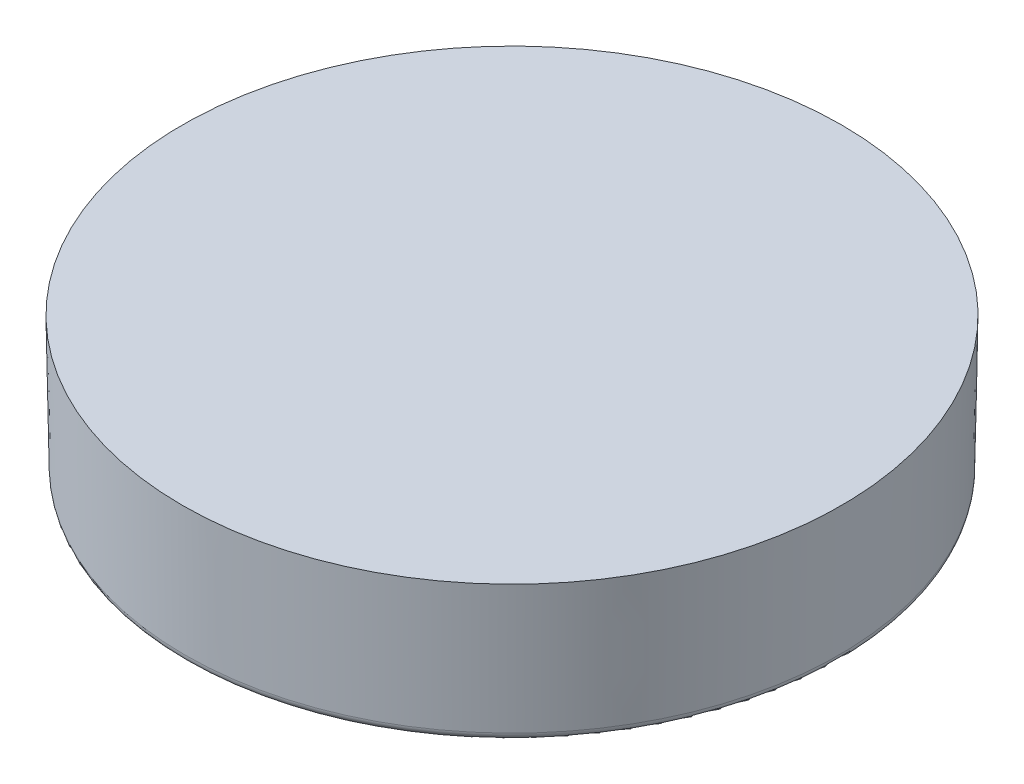
SolidWorks part; units mm, degrees
material "CA"
ref_plane "Front Plane" through (0, 0, 0) normal (0, 0, 1) x (1, 0, 0)
ref_plane "Top Plane" through (0, 0, 0) normal (0, 1, 0) x (1, 0, 0)
ref_plane "Right Plane" through (0, 0, 0) normal (1, 0, 0) x (0, 0, -1)
sketch "Sketch1" plane through (0, 0, 0) normal (0, 1, 0) x (1, 0, 0)
  circle A0 centre (0, 0) radius 15.0813
  dimension "D1" = 30.1625
extrude "Boss-Extrude1" add sketch "Sketch1" against normal blind 2.3114 draft 1
sketch "Sketch6" plane through (0, 0, 0) normal (0, 0, 1) x (1, 0, 0)
  line L0 (0, 0) -> (0, -2.54) construction
  line L1 (0, -2.54) -> (-6.985, -9.525)
  line L2 (0, -2.54) -> (6.985, -9.525)
  line L3 (-6.985, -9.525) -> (6.985, -9.525)
  line L5 (15.0813, 0) -> (-15.0813, 0) construction
  dimension "D1" = 2.54
  dimension "D2" = 90
  dimension "D3" = 9.525
sketch "Sketch7" plane through (0, 0, 0) normal (0, 1, 0) x (1, 0, 0)
  circle A1 centre (0, 0) radius 15.0813
  circle A2 centre (0, 0) radius 15.0813
  circle A3 centre (0, 0) radius 13.3033
  circle A4 centre (0, 0) radius 13.3033
  dimension "D1" = 0
  dimension "D2" = 1.778
extrude "Boss-Extrude3" add sketch "Sketch7" against normal blind 6.35 draft 1
draft "Draft1" type of draft neutral plane draft angle 10 faces to draft 1 face at (0, -6.35, 13.4141) neutral plane through (0, -2.3114, 0) neutral plane normal (0, -1, 0) parameters "D1"=10
fillet "Fillet2" radius 0.381 2 edges at (0, -6.35, 14.0557) (0, -6.35, 14.9704)
sketch "Sketch11 - OFFSET .005" plane through (0, 0, 0) normal (0, 1, 0) x (1, 0, 0)
  circle A1 centre (0, 0) radius 15.2083
  circle A2 centre (0, 0) radius 15.2083
  dimension "D1" = 0.127
